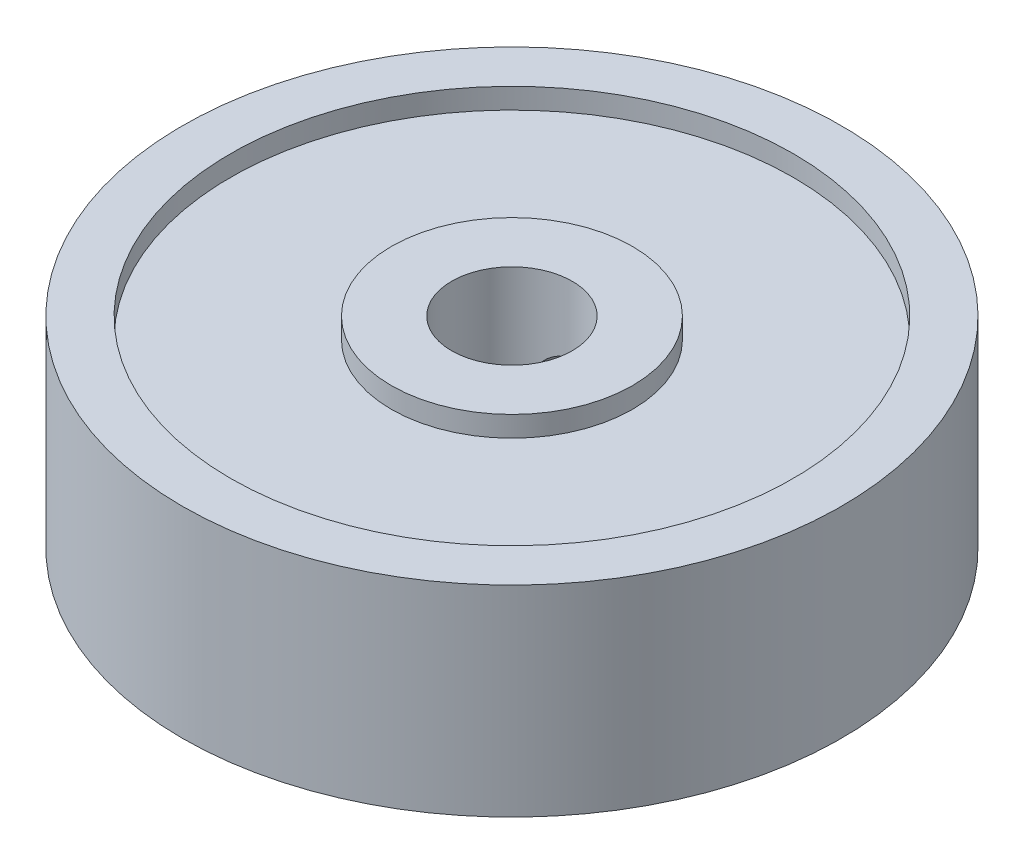
SolidWorks part; units mm, degrees
material "Cast Alloy Steel"
ref_plane "Front Plane" through (0, 0, 0) normal (0, 0, 1) x (1, 0, 0)
ref_plane "Top Plane" through (0, 0, 0) normal (0, 1, 0) x (1, 0, 0)
ref_plane "Right Plane" through (0, 0, 0) normal (1, 0, 0) x (0, 0, -1)
sketch "Sketch1" plane through (0, 0, 0) normal (0, 1, 0) x (1, 0, 0)
  circle A0 centre (0, 0) radius 13.0175
  circle A1 centre (0, 0) radius 2.3813
  dimension "D1" = 26.035
  dimension "D2" = 4.7625
extrude "Boss-Extrude1" add sketch "Sketch1" along normal blind 7.9375
sketch "Sketch2" plane through (0, 7.9375, 0) normal (0, 1, 0) x (1, 0, 0)
  circle A0 centre (0, 0) radius 11.1125
  circle A1 centre (0, 0) radius 4.7625
  dimension "D1" = 22.225
  dimension "D2" = 9.525
extrude "Cut-Extrude1" cut sketch "Sketch2" against normal blind 0.8128
sketch "Sketch3" plane through (0, 0, 0) normal (0, -1, 0) x (1, 0, 0)
  circle A0 centre (0, 0) radius 11.1125
  circle A1 centre (0, 0) radius 4.7625
  dimension "D1" = 9.525
  dimension "D2" = 22.225
extrude "Cut-Extrude2" cut sketch "Sketch3" against normal blind 0.8128
sketch "Sketch4" plane through (0, 0, 0) normal (0, 0, 1) x (1, 0, 0)
  circle A0 centre (0, 3.9624) radius 1.2891
  dimension "D2" = 2.5781
  dimension "D1" = 3.9624
extrude "Cut-Extrude3" cut sketch "Sketch4" against normal through all
